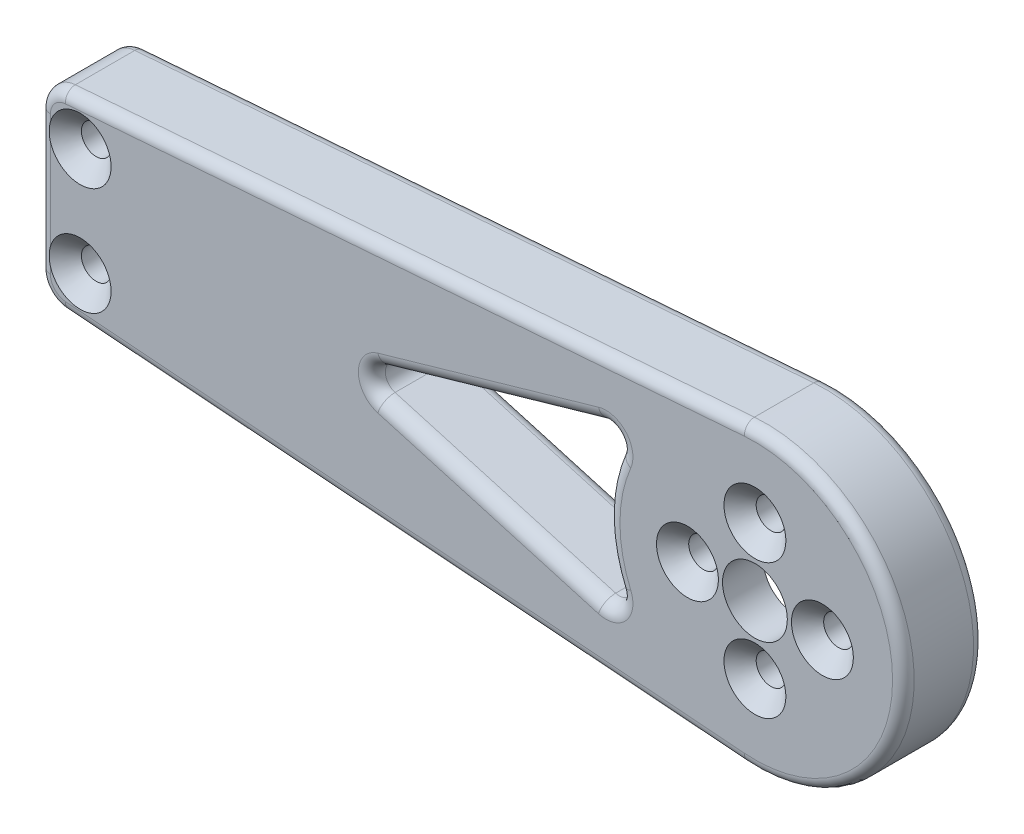
SolidWorks part; units mm, degrees
material "ABS"
ref_plane "Front Plane" through (0, 0, 0) normal (0, 0, 1) x (1, 0, 0)
ref_plane "Top Plane" through (0, 0, 0) normal (0, 1, 0) x (1, 0, 0)
ref_plane "Right Plane" through (0, 0, 0) normal (1, 0, 0) x (0, 0, -1)
sketch "Sketch1" plane through (0, 0, 0) normal (0, 0, 1) x (1, 0, 0)
  line L0 (0, 0) -> (-125, 0) construction
  line L1 (-125, -10) -> (-125, 10) construction
  line L2 (-2.0859, -27.4208) -> (-127.8793, -17.8515)
  line L3 (-132.5, 17.5) -> (-117.5, 17.5) construction
  line L4 (-132.5, 17.5) -> (-132.5, -17.5) construction
  line L5 (-132.5, -17.5) -> (-117.5, -17.5) construction
  line L6 (-117.5, 17.5) -> (-117.5, -17.5) construction
  line L7 (-132.5, 17.5) -> (-117.5, -17.5) construction
  line L8 (-132.5, -17.5) -> (-117.5, 17.5) construction
  line L9 (-132.5, -12.8659) -> (-132.5, 12.8659)
  line L10 (-127.8793, 17.8515) -> (-2.0859, 27.4208)
  circle A0 centre (0, 0) radius 6
  circle A1 centre (0, 0) radius 27.5 construction
  circle A2 centre (-125, 10) radius 2.5 construction
  circle A3 centre (-125, -10) radius 2.5 construction
  arc A4 (-2.0859, 27.4208) -> (-2.0859, -27.4208) centre (0, 0) cw
  arc A5 (-132.5, 12.8659) -> (-127.8793, 17.8515) centre (-127.5, 12.8659) cw
  arc A6 (-127.8793, -17.8515) -> (-132.5, -12.8659) centre (-127.5, -12.8659) cw
  point P8 (-125, 0)
  dimension "D1" = 12
  dimension "D2" = 55
  dimension "D5" = 5
  dimension "D6" = 5
  dimension "D9" = 5
  dimension "D3" = 125
  dimension "D4" = 20
  dimension "D7" = 35
  dimension "D8" = 15
  dimension "D10" = 132.5
extrude "Boss-Extrude1" add sketch "Sketch1" along normal mid plane 15
sketch "Sketch2" plane through (0, 0, -7.5) normal (0, 0, -1) x (-1, 0, 0)
  circle A0 centre (0, 0) radius 20
  dimension "D1" = 40
extrude "Cut-Extrude1" cut sketch "Sketch2" against normal blind 7.5
sketch "Sketch3" plane through (0, 0, 0) normal (0, 0, -1) x (-1, 0, 0)
  line L0 (20, 0) -> (-20, 0) construction
  line L1 (-20, 0) -> (0, 20) construction
  line L2 (0, 20) -> (0, -20) construction
  circle A0 centre (0, 0) radius 20 construction
  circle A1 centre (0, 0) radius 20 construction
  circle A2 centre (0, 12.5) radius 2.5
  circle A3 centre (0, -12.5) radius 2.5
  circle A4 centre (12.5, 0) radius 2.5
  circle A5 centre (-12.5, 0) radius 2.5
  dimension "D1" = 5
  dimension "D2" = 25
  dimension "D3" = 25
extrude "Cut-Extrude2" [suppressed] cut sketch "Sketch3" against normal blind 5
other "Graphic1" [suppressed]
other "Graphic (Closed) -1"
imported_body "Imported2" [suppressed]
other "Graphic2" [suppressed]
other "Graphic (Closed) -2"
imported_body "Imported3" [suppressed]
sketch "Sketch4" plane through (0, 0, -7.5) normal (0, 0, -1) x (-1, 0, 0)
  line L0 (0, 0) -> (132.5, 0) construction
  line L1 (132.5, 12.8659) -> (132.5, -12.8659) construction
  line L2 (28.2882, 14.1682) -> (69.1554, 2.4024)
  line L3 (69.1554, -2.4024) -> (28.2882, -14.1682)
  line L4 (2.0859, 27.4208) -> (127.8793, 17.8515) construction
  circle A0 centre (0, 0) radius 27.5 construction
  arc A2 (25.2968, -10.7853) -> (25.2968, 10.7853) centre (0, 0) ccw
  arc A3 (69.1554, 2.4024) -> (69.1554, -2.4024) centre (68.4638, 0) cw
  arc A4 (28.2882, -14.1682) -> (25.2968, -10.7853) centre (27.5965, -11.7658) cw
  arc A5 (28.2882, 14.1682) -> (25.2968, 10.7853) centre (27.5965, 11.7658) ccw
  point P19 (77.5, 0)
  point P22 (22.4795, -15.8405)
  point P25 (22.4795, 15.8405)
  dimension "D3" = 2.5
  dimension "D4" = 55
  dimension "D1" = 10
  dimension "D2" = 55
extrude "Cut-Extrude3" cut sketch "Sketch4" against normal through all
sketch "Sketch6" plane through (0, 0, -7.5) normal (0, 0, -1) x (-1, 0, 0)
  line L0 (-27.5, 0) -> (132.5, 0) construction
  line L1 (132.5, 12.8659) -> (132.5, -12.8659) construction
  line L2 (58.6316, 10.6353) -> (79.3555, 4.6689)
  line L3 (82.5472, 7.0713) -> (82.5472, 11.4613)
  line L4 (80.2368, 13.9541) -> (59.5129, 15.5306)
  line L5 (2.0859, 27.4208) -> (127.8793, 17.8515) construction
  line L6 (69.1554, 2.4024) -> (28.2882, 14.1682) construction
  arc A0 (2.0859, 27.4208) -> (2.0859, -27.4208) centre (0, 0) ccw construction
  arc A1 (82.5472, 11.4613) -> (80.2368, 13.9541) centre (80.0472, 11.4613) ccw
  arc A2 (79.3555, 4.6689) -> (82.5472, 7.0713) centre (80.0472, 7.0713) ccw
  arc A3 (58.6316, 10.6353) -> (59.5129, 15.5306) centre (59.3233, 13.0378) cw
  point P18 (82.5472, 3.75)
  dimension "D4" = 2.5
  dimension "D1" = 5
  dimension "D2" = 7.5
  dimension "D3" = 7.5
extrude "Cut-Extrude5" cut sketch "Sketch6" against normal blind 10
sketch "Sketch7" plane through (0, 0, -7.5) normal (0, 0, -1) x (-1, 0, 0)
  line L0 (132.5, 0) -> (70.9638, 0) construction
  line L1 (132.5, 12.8659) -> (132.5, -12.8659) construction
  line L2 (87.5472, 6.7994) -> (87.5472, 10.7006)
  line L3 (90.2368, 13.1933) -> (104.3701, 12.1182)
  line L4 (104.6706, 7.1739) -> (90.5374, 4.3479)
  line L5 (82.5472, 7.0713) -> (82.5472, 11.4613) construction
  line L6 (80.2368, 13.9541) -> (59.5129, 15.5306) construction
  arc A0 (69.1554, -2.4024) -> (69.1554, 2.4024) centre (68.4638, 0) ccw construction
  arc A1 (104.3701, 12.1182) -> (104.6706, 7.1739) centre (104.1804, 9.6254) cw
  arc A2 (87.5472, 6.7994) -> (90.5374, 4.3479) centre (90.0472, 6.7994) ccw
  arc A3 (87.5472, 10.7006) -> (90.2368, 13.1933) centre (90.0472, 10.7006) cw
  point P16 (122.5, 10.739)
  point P19 (87.5472, 3.75)
  dimension "D4" = 2.5
  dimension "D1" = 5
  dimension "D2" = 10
  dimension "D3" = 7.5
extrude "Cut-Extrude6" cut sketch "Sketch7" against normal blind 10
sketch "Sketch8" plane through (0, 0, -7.5) normal (0, 0, -1) x (-1, 0, 0)
  line L0 (132.5, 0) -> (-27.5, 0) construction
  line L1 (132.5, 12.8659) -> (132.5, -12.8659) construction
  line L2 (106.5536, -2.4515) -> (114.5098, -4.0424)
  line L3 (117.5, -1.5909) -> (117.5, 1.5909)
  line L4 (114.5098, 4.0424) -> (106.5536, 2.4515)
  line L5 (90.5374, 4.3479) -> (104.6706, 7.1739) construction
  arc A0 (2.0859, 27.4208) -> (2.0859, -27.4208) centre (0, 0) ccw construction
  arc A1 (114.5098, -4.0424) -> (117.5, -1.5909) centre (115, -1.5909) ccw
  arc A2 (117.5, 1.5909) -> (114.5098, 4.0424) centre (115, 1.5909) ccw
  arc A3 (106.5536, -2.4515) -> (106.5536, 2.4515) centre (107.0437, 0) cw
  point P11 (117.5, 0)
  point P19 (94.2935, 0)
  dimension "D3" = 2.5
  dimension "D1" = 5
  dimension "D2" = 15
extrude "Cut-Extrude7" cut sketch "Sketch8" against normal blind 10
sketch "Sketch10" plane through (0, 0, -7.5) normal (0, 0, -1) x (-1, 0, 0)
  line L0 (69.1554, 2.4024) -> (28.2882, 14.1682) construction
  line L1 (28.2882, -14.1682) -> (69.1554, -2.4024) construction
  line L2 (49.3383, 8.1078) -> (54.6035, 6.5919)
  line L3 (54.6035, -6.5919) -> (49.3383, -8.1078)
  circle A0 centre (0, 0) radius 50 construction
  arc A1 (49.3383, 8.1078) -> (49.3383, -8.1078) centre (0, 0) cw
  circle A2 centre (0, 0) radius 55 construction
  arc A3 (54.6035, 6.5919) -> (54.6035, -6.5919) centre (0, 0) cw
  dimension "D1" = 100
  dimension "D2" = 5
sketch "Sketch9" plane through (0, 0, 0) normal (0, 0, 1) x (1, 0, 0)
  line L0 (-2.0859, 27.4208) -> (-7.4508, 32.0271)
  line L1 (-7.4508, 32.0271) -> (-122.1195, 23.3041)
  line L2 (-122.1195, 23.3041) -> (-126.7258, 17.9392)
  line L3 (-2.0859, 27.4208) -> (-127.8793, 17.8515) construction
  line L4 (-126.7258, 17.9392) -> (-2.0859, 27.4208)
  arc A0 (-2.0859, -27.4208) -> (-2.0859, 27.4208) centre (0, 0) ccw construction
  dimension "D1" = 45
  dimension "D2" = 45
  dimension "D3" = 5
  dimension "D4" = 125
extrude "Boss-Extrude2" [suppressed] add sketch "Sketch9" along normal mid plane 10
mirror "Mirror1" about plane through (0, 0, 0) normal (0, 1, 0) of "Cut-Extrude6", "Cut-Extrude5"
fillet "Fillet2" [suppressed] radius 5
fillet "Fillet3" radius 2.5 36 edges at (-69.8749, -14.7423, 2.5) (-56.8628, -13.4807, 2.5) (-68.9936, -7.6521, 2.5) (-81.5507, -5.0739, 2.5) (-82.5472, -9.2663, 2.5) (-81.8808, -13.1607, 2.5) (-97.3034, -12.6558, 2.5) (-88.3478, -12.5341, 2.5) (-87.5472, -8.75, 2.5) (-88.4622, -4.8661, 2.5) (-97.604, -5.7609, 2.5) (-106.6758, -9.7771, 2.5) (-110.5317, -3.2469, 2.5) (-104.5437, 0, 2.5) (-110.5317, 3.2469, 2.5) (-116.585, 3.5242, 2.5) (-117.5, 0, 2.5) (-116.585, -3.5242, 2.5) (-97.604, 5.7609, 2.5) (-88.4622, 4.8661, 2.5) (-87.5472, 8.75, 2.5) (-88.3478, 12.5341, 2.5) (-97.3034, 12.6558, 2.5) (-106.6758, 9.7771, 2.5) (-82.5472, 9.2663, 2.5) (-81.5507, 5.0739, 2.5) (-68.9936, 7.6521, 2.5) (-56.8628, 13.4807, 2.5) (-69.8749, 14.7423, 2.5) (-81.8808, 13.1607, 2.5) (-25.7237, 13.4218, 7.5) (-48.7218, 8.2853, 7.5) (-70.9638, 0, 7.5) (-48.7218, -8.2853, 7.5) (-25.7237, -13.4218, 7.5) (-27.5, 0, 7.5)
fillet "Fillet4" radius 2 48 edges at (-88.4622, -4.8661, -7.5) (-87.5472, -8.75, -7.5) (-88.3478, -12.5341, -7.5) (-97.3034, -12.6558, -7.5) (-106.6758, -9.7771, -7.5) (-116.585, 3.5242, -7.5) (-117.5, 0, -7.5) (-116.585, -3.5242, -7.5) (-110.5317, -3.2469, -7.5) (-104.5437, 0, -7.5) (-106.6758, 9.7771, -7.5) (-97.604, 5.7609, -7.5) (-88.4622, 4.8661, -7.5) (-87.5472, 8.75, -7.5) (-88.3478, 12.5341, -7.5) (-56.8628, -13.4807, -7.5) (-69.8749, -14.7423, -7.5) (-81.8808, -13.1607, -7.5) (-82.5472, -9.2663, -7.5) (-81.5507, -5.0739, -7.5) (-70.9638, 0, -7.5) (-48.7218, -8.2853, -7.5) (-81.8808, 13.1607, -7.5) (-82.5472, 9.2663, -7.5) (-81.5507, 5.0739, -7.5) (-68.9936, 7.6521, -7.5) (-56.8628, 13.4807, -7.5) (-25.7237, 13.4218, -7.5) (-48.7218, 8.2853, -7.5) (-25.7237, -13.4218, -7.5) (-97.604, -5.7609, -7.5) (-110.5317, 3.2469, -7.5) (-97.3034, 12.6558, -7.5) (-68.9936, -7.6521, -7.5) (-69.8749, 14.7423, -7.5) (-27.5, 0, -7.5) (-64.9826, -22.6361, 7.5) (-131.1672, -16.2647, 7.5) (-132.5, 0, 7.5) (-131.1672, 16.2647, 7.5) (-64.9826, 22.6361, 7.5) (27.5, 0, 7.5) (27.5, 0, -7.5) (-64.9826, -22.6361, -7.5) (-131.1672, -16.2647, -7.5) (-132.5, 0, -7.5) (-131.1672, 16.2647, -7.5) (-64.9826, 22.6361, -7.5)
hole_wizard "CSK for M5 Hex Socket Countersunk Head Screw1" positions "Sketch11" profile "Sketch12" countersink size "M5" standard "DIN" end condition through all
sketch "Sketch11" plane through (0, 0, 7.5) normal (0, 0, 1) x (1, 0, 0)
  circle A0 centre (0, 0) radius 12.5 construction
  point P4 (0, 12.5)
  point P10 (12.5, 0)
  point P11 (0, -12.5)
  point P12 (-12.5, 0)
  dimension "D1" = 25
  dimension "D2" = 4
sketch "Sketch12" plane through (-12.5, 0, 7.5) normal (1, 0, 0) x (0, -1, 0)
  line L0 (0, 0) -> (0, 15)
  line L1 (0, 15) -> (2.75, 15)
  line L2 (2.75, 15) -> (2.75, 2.985)
  line L3 (2.75, 2.985) -> (5.735, 0)
  line L5 (5.735, 0) -> (0, 0)
  line L6 (-2.75, 2.985) -> (-5.735, 0) construction
  line L11 (0, -6.35) -> (0, 107.95) construction
  dimension "Thru Hole Dia." = 5.5
  dimension "Thru Hole Depth" = 15
  dimension "Near C'Sink Dia." = 11.47
  dimension "Near C'Sink Angle" = 90
hole_wizard "CSK for M5 Hex Socket Countersunk Head Screw2" positions "Sketch13" profile "Sketch14" countersink size "M5" standard "DIN" end condition through all
sketch "Sketch13" plane through (0, 0, 7.5) normal (0, 0, 1) x (1, 0, 0)
  line L2 (-125, 10) -> (-125, -10) construction
  line L4 (-132.5, -12.8659) -> (-132.5, 12.8659) construction
  line L5 (-132.5, 0) -> (27.5, 0) construction
  arc A0 (-2.0859, -27.4208) -> (-2.0859, 27.4208) centre (0, 0) ccw construction
  point P0 (-125, 10)
  point P2 (-125, -10)
  dimension "D1" = 20
  dimension "D2" = 7.5
  dimension "D3" = 10
sketch "Sketch14" plane through (-125, 10, 7.5) normal (1, 0, 0) x (0, -1, 0)
  line L0 (0, 0) -> (0, 15)
  line L1 (0, 15) -> (2.75, 15)
  line L2 (2.75, 15) -> (2.75, 2.985)
  line L3 (2.75, 2.985) -> (5.735, 0)
  line L5 (5.735, 0) -> (0, 0)
  line L6 (-2.75, 2.985) -> (-5.735, 0) construction
  line L11 (0, -6.35) -> (0, 107.95) construction
  dimension "Thru Hole Dia." = 5.5
  dimension "Thru Hole Depth" = 15
  dimension "Near C'Sink Dia." = 11.47
  dimension "Near C'Sink Angle" = 90
